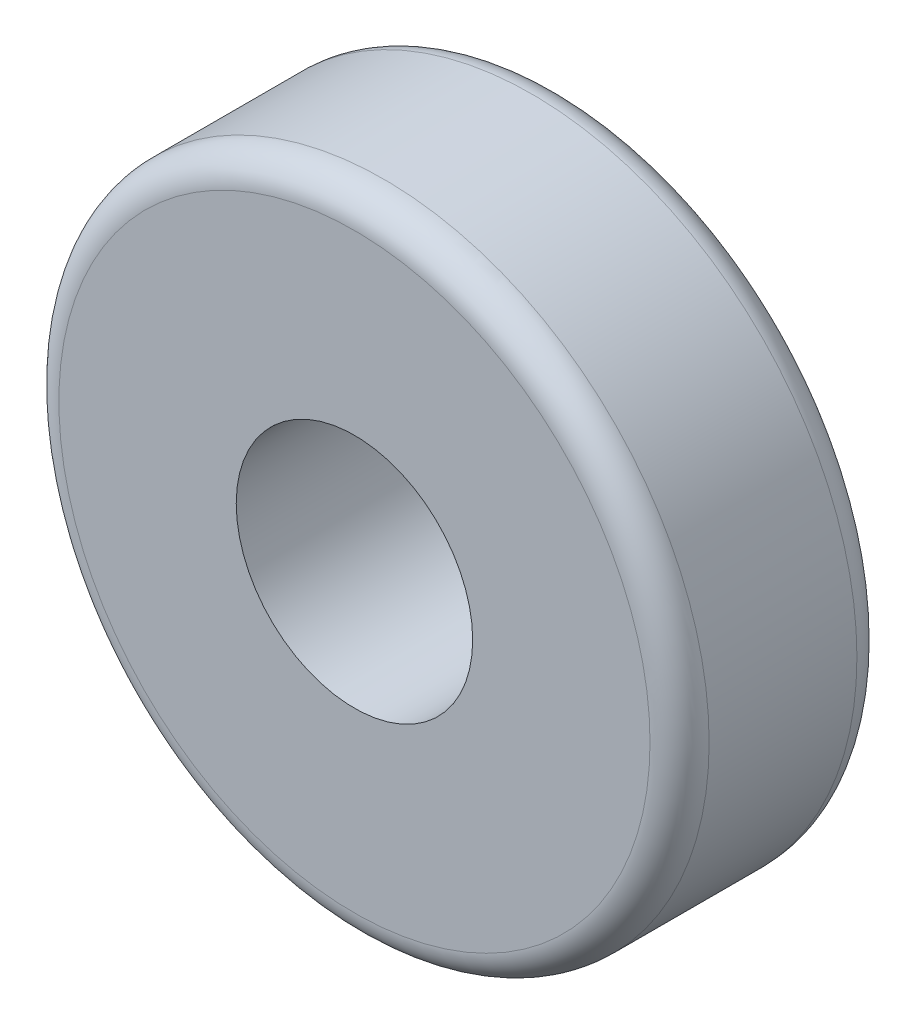
SolidWorks part; units mm, degrees
ref_plane "Plano frontal" through (0, 0, 0) normal (0, 0, 1) x (1, 0, 0)
ref_plane "Plano superior" through (0, 0, 0) normal (0, 1, 0) x (1, 0, 0)
ref_plane "Plano direito" through (0, 0, 0) normal (1, 0, 0) x (0, 0, -1)
sketch "Esboço1" plane through (0, 0, 0) normal (0, 0, 1) x (1, 0, 0)
  circle A0 centre (0, 0) radius 11
  circle A1 centre (0, 0) radius 4
  dimension "D1" = 8
  dimension "D2" = 22
extrude "Ressalto-extrusão1" add sketch "Esboço1" along normal blind 7
fillet "Filete1" radius 1 2 edges at (11, 0, 0) (11, 0, 7)
